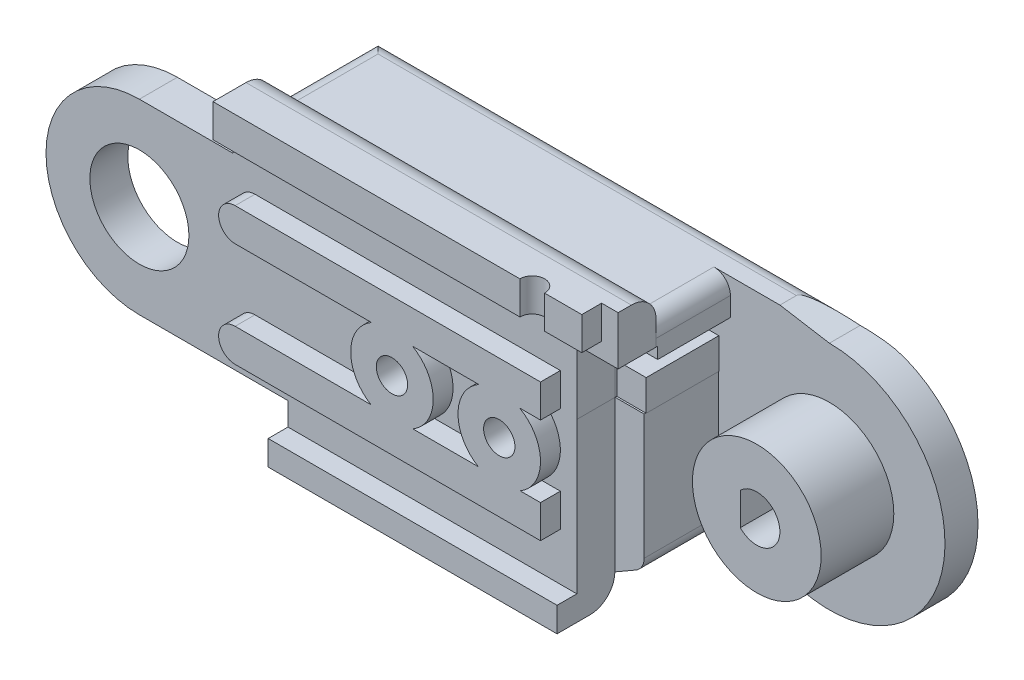
SolidWorks part; units mm, degrees
ref_plane "Front Plane" through (0, 0, 0) normal (0, 0, 1) x (1, 0, 0)
ref_plane "Top Plane" through (0, 0, 0) normal (0, 1, 0) x (1, 0, 0)
ref_plane "Right Plane" through (0, 0, 0) normal (1, 0, 0) x (0, 0, -1)
sketch "Sketch3" plane through (0, 0, 0) normal (0, 0, 1) x (1, 0, 0)
  line L7 (8, 0) -> (9, -2.5431)
  line L11 (35, 6.9569) -> (32, 7.4569)
  line L18 (5.6569, 5.6569) -> (5.6569, 7.4569)
  line L19 (5.6569, 7.4569) -> (32, 7.4569)
  line L20 (26.5, -7.0431) -> (9, -7.0431)
  line L21 (9, -7.0431) -> (9, -2.5431)
  line L23 (30.0502, -4.9929) -> (26.5, -7.0431)
  arc A4 (8, 0) -> (5.6569, 5.6569) centre (0, 0) ccw
  arc A5 (30.0502, -4.9929) -> (35, 6.9569) centre (35, -0.0431) ccw
  dimension "D3" = 3.5503
  dimension "D10" = 2.5431
  dimension "D17" = 14
  dimension "D4" = 5.6569
  dimension "D5" = 135
  dimension "D2" = 35
  dimension "D6" = 14.5
  dimension "D7" = 4.5
  dimension "D8" = 1
  dimension "D9" = 45
  dimension "D11" = 1.8
  dimension "D14" = 3
extrude "Boss-Extrude1" add sketch "Sketch3" along normal blind 2 contours A5 L11 L19 L18 A4 L7 L21 L20 L23
sketch "Sketch20" plane through (0, 0, 0) normal (0, 0, 1) x (1, 0, 0)
  line L0 (0, 7) -> (0, 7.5) construction
  line L1 (0, 7.5) -> (-19.4737, 7.5) construction
  line L2 (0, 5.3) -> (-14, 5.3) construction
  line L3 (0, 4) -> (-14, 4) construction
  line L4 (-14, 4) -> (-14, 5.3) construction
  line L5 (0, 5.3) -> (17.4849, 5.3) construction
  line L6 (17.4849, 5.3) -> (17.4849, 4) construction
  line L7 (17.4849, 4) -> (0, 4) construction
  line L8 (-2.5, 7.5) -> (-2.5, 2.868) construction
  circle A0 centre (0, 0) radius 7 construction
  circle A1 centre (0, 0) radius 3.9 construction
  circle A3 centre (0, 0) radius 5.3 construction
  circle A4 centre (0, 0) radius 4 construction
  circle A5 centre (0, 0) radius 2 construction
  dimension "D1" = 0
  dimension "D2" = 2.5
ref_plane "Plane1" through (0, 0, 2) normal (0, 0, 1) x (1, 0, 0)
sketch "Sketch4" plane through (0, 0, 2) normal (0, 0, 1) x (1, 0, 0)
  line L4 (5.6569, 5.6569) -> (5.6569, 7.5)
  line L5 (5.6569, 5.6569) -> (5.6569, 7.4569) construction
  line L6 (5.6569, 7.5) -> (26.5, 7.5)
  line L10 (8, 0) -> (9, -2.5431)
  line L11 (9, -2.5431) -> (9, -7.0431)
  line L12 (9, -7.0431) -> (26.5, -7.0431)
  line L13 (26.5, -7.0431) -> (26.5, 7.5)
  arc A0 (8, 0) -> (5.6569, 5.6569) centre (0, 0) ccw construction
  arc A3 (8, 0) -> (5.6569, 5.6569) centre (0, 0) ccw
sketch "Sketch22" plane through (0, 0, 2) normal (0, 0, 1) x (1, 0, 0)
  line L1 (5.6569, 7.4569) -> (26.5, 7.4569)
  line L6 (8, 0) -> (9, -2.5431)
  line L7 (9, -2.5431) -> (9, -7.0431)
  line L8 (9, -7.0431) -> (26.5, -7.0431)
  line L10 (26.5, 7.4569) -> (32, 7.4569)
  line L11 (32, 7.4569) -> (32, 2.1289)
  line L12 (32, 2.1289) -> (28.2751, 2.1289)
  line L13 (26.5, -7.0431) -> (28.2751, -6.018)
  line L14 (30.0502, -4.9929) -> (26.5, -7.0431) construction
  line L15 (28.2751, -6.018) -> (28.2751, 2.1289)
  line L16 (5.6569, 7.4569) -> (5.6569, 5.6569)
  arc A0 (8, 0) -> (5.6569, 5.6569) centre (0, 0) ccw
  dimension "D1" = 5.328
extrude "Boss-Extrude6" add sketch "Sketch22" along normal blind 4.5
sketch "Sketch25" plane through (0, 0, 2) normal (0, 0, 1) x (1, 0, 0)
  line L0 (0, 5.3) -> (18.0981, 5.3) construction
  line L1 (0, 4) -> (18.0981, 4) construction
  line L2 (18.0981, 4) -> (18.0981, 5.3) construction
sketch "Sketch26" plane through (0, 0, 2) normal (0, 0, 1) x (1, 0, 0)
  line L1 (18.0981, 5.3) -> (2.5301, 5.3)
  line L2 (18.0981, 4) -> (2.5301, 4)
  line L3 (2.5301, 5.3) -> (2.5301, 4)
  line L4 (18.0981, 5.3) -> (32, 5.3)
  line L5 (32, 2.1289) -> (32, 7.4569) construction
  line L6 (32, 5.3) -> (32, 4)
  line L7 (32, 4) -> (18.0981, 4)
extrude "Cut-Extrude6" cut sketch "Sketch26" along normal blind 4.5
ref_plane "Plane18" through (0, 0, 6.5) normal (0, 0, 1) x (1, 0, 0)
sketch "Sketch31" plane through (0, 0, 6.5) normal (0, 0, 1) x (1, 0, 0)
  line L0 (2.4327, 5.6569) -> (0, 5.6569)
  line L4 (9, -5.6569) -> (0, -5.6569)
  line L7 (2.4327, 5.6569) -> (5.6569, 5.6569)
  line L8 (5.6569, 5.6569) -> (5.6569, 7.4569)
  line L12 (9, -7.0431) -> (9, -5.6569)
  line L13 (9, -2.5431) -> (9, -7.0431) construction
  line L16 (32, 7.4569) -> (32, 2.1289)
  line L17 (32, 2.1289) -> (28.2751, 2.1289)
  line L22 (5.6569, 7.4569) -> (5.6569, 8.9569)
  line L23 (5.6569, 8.9569) -> (32, 8.9569)
  line L24 (32, 8.9569) -> (32, 7.4569)
  line L25 (9, -7.0431) -> (9, -8.5431)
  line L26 (9, -8.5431) -> (26.5, -8.5431)
  line L27 (26.5, -8.5431) -> (26.5, -7.0431)
  line L28 (26.5, -7.0431) -> (26.5, 2.1289)
  line L29 (26.5, 2.1289) -> (28.2751, 2.1289)
  line L30 (9, -7.0431) -> (26.5, -7.0431) construction
  line L31 (32, 7.4569) -> (5.6569, 7.4569) construction
  arc A0 (0, 5.6569) -> (0, -5.6569) centre (0, 0) ccw
  dimension "D1" = 5.6569
  dimension "D2" = 5.6569
  dimension "D3" = 1.5
  dimension "D4" = 1.5
extrude "Boss-Extrude14" add sketch "Sketch31" along normal blind 2.3 separate body
sketch "Sketch32" plane through (0, 0, 8.8) normal (0, 0, 1) x (1, 0, 0)
  circle A0 centre (0, 0) radius 3
  dimension "D1" = 6
extrude "Cut-Extrude7" cut sketch "Sketch32" against normal blind 2.3
sketch "Sketch33" plane through (0, 0, 8.8) normal (0, 0, 1) x (1, 0, 0)
  line L1 (5.6569, 8.9569) -> (5.6569, 6.9569)
  line L4 (9, -7.0431) -> (9, -8.5431)
  line L7 (7, -4.1569) -> (25.5, -4.1569)
  line L11 (9, -8.5431) -> (26.5, -8.5431)
  line L15 (26.5, -8.5431) -> (26.5, -7.0431)
  line L16 (26.5, -7.0431) -> (9, -7.0431)
  line L17 (5.6569, 8.9569) -> (28, 8.9569)
  line L18 (32, 8.9569) -> (5.6569, 8.9569) construction
  line L21 (28, 6.9569) -> (28, 8.9569)
  line L22 (25.5, -4.1569) -> (25.5, -2.1569)
  line L23 (25.5, -2.1569) -> (7, -2.1569)
  line L27 (5.6569, 6.9569) -> (28, 6.9569)
  line L28 (25.5, 2.172) -> (7, 2.172)
  line L30 (7, 4.172) -> (25.5, 4.172)
  line L33 (25.5, 2.172) -> (25.5, 4.172)
  line L34 (32, 2.1289) -> (32, 8.9569) construction
  line L35 (9, -8.5431) -> (26.5, -8.5431) construction
  line L37 (26.5, -8.5431) -> (26.5, 2.1289) construction
  arc A1 (7, -2.1569) -> (7, -4.1569) centre (7, -3.1569) ccw
  arc A2 (7, 4.172) -> (7, 2.172) centre (7, 3.172) ccw
  dimension "D1" = 1.5
  dimension "D2" = 2
  dimension "D3" = 2
  dimension "D5" = 2
  dimension "D6" = 2.5
  dimension "D8" = 4
extrude "Boss-Extrude15" add sketch "Sketch33" along normal blind 1.2
sketch "Sketch34" plane through (0, 0, 2) normal (0, 0, 1) x (1, 0, 0)
  line L0 (35, 5.3) -> (18.0981, 5.3) construction
  line L1 (35, 4) -> (18.0981, 4) construction
  circle A0 centre (35, -0.0431) radius 2 construction
  circle A1 centre (35, -0.0431) radius 5.3431 construction
  circle A2 centre (35, -0.0431) radius 4.0431 construction
sketch "Sketch35" plane through (0, 0, 8.8) normal (0, 0, 1) x (1, 0, 0)
  line L0 (32, 2.1289) -> (32, 6)
  line L1 (32, 2.1289) -> (26.5203, 2.1289)
  line L2 (32, 6) -> (26.5203, 6)
  line L3 (26.5203, 2.1289) -> (26.5203, 6)
  line L4 (32, 2.1289) -> (32, 8.9569) construction
  dimension "D1" = 5.4796
extrude "Cut-Extrude8" cut sketch "Sketch35" against normal blind 2.4
sketch "Sketch36" plane through (0, 0, 6.4) normal (0, 0, 1) x (1, 0, 0)
  line L0 (32, 2.1289) -> (32, 4)
  line L1 (32, 2.1289) -> (28.3, 2.1289)
  line L2 (32, 4) -> (28.3, 4)
  line L3 (28.3, 2.1289) -> (28.3, 4)
  line L4 (26.5, -7.0431) -> (26.5, 7.5) construction
  dimension "D1" = 1.8
extrude "Cut-Extrude9" cut sketch "Sketch36" against normal blind 4.4
sketch "Sketch37" plane through (0, 0, 2) normal (0, 0, 1) x (1, 0, 0)
  circle A0 centre (35, -0.0431) radius 3.9
  dimension "D1" = 7.8
extrude "Boss-Extrude16" add sketch "Sketch37" along normal blind 4.4
sketch "Sketch39" plane through (0, 0, 6.4) normal (0, 0, 1) x (1, 0, 0)
  line L0 (34, 0.9367) -> (34, -1.0229)
  arc A0 (34, -1.0229) -> (34, 0.9367) centre (35, -0.0431) ccw
  dimension "D2" = 2.8
  dimension "D1" = 1
extrude "Cut-Extrude10" cut sketch "Sketch39" against normal through all
sketch "Sketch43" plane through (0, 0, 8.8) normal (0, 0, 1) x (1, 0, 0)
  line L2 (0, -5.6569) -> (9, -5.6569) construction
  circle A0 centre (16.5, 0) radius 2.5
  circle A1 centre (23, 0) radius 2.5
  dimension "D1" = 7.5
  dimension "D3" = 5
  dimension "D4" = 6.5
  dimension "D2" = 5.6569
extrude "Boss-Extrude17" add sketch "Sketch43" along normal blind 1.2
sketch "Sketch44" plane through (0, 0, 10) normal (0, 0, 1) x (1, 0, 0)
  circle A0 centre (16.5, 0) radius 0.95
  circle A1 centre (23, 0) radius 0.95
  dimension "D1" = 1.9
  dimension "D2" = 1.9
extrude "Cut-Extrude11" cut sketch "Sketch44" against normal through all
sketch "Sketch45" plane through (0, 0, 0) normal (0, 0, -1) x (-1, 0, 0)
  circle A0 centre (-16.5, 0) radius 2
  circle A1 centre (-23, 0) radius 2
extrude "Cut-Extrude12" cut sketch "Sketch45" against normal blind 4.5
ref_plane "Plane17" through (0, 0, 10) normal (0, 0, 1) x (1, 0, 0)
sketch "Sketch48" plane through (0, 0, 2) normal (0, 0, 1) x (1, 0, 0)
  circle A0 centre (35, -0.0431) radius 6 construction
  dimension "D1" = 12
sketch "Sketch49" plane through (0, 6.9569, 0) normal (0, -1, 0) x (1, 0, 0)
  line L0 (5.6569, 10) -> (28, 10) construction
  line L1 (28, 10) -> (28, 8.8) construction
  line L2 (5.6569, 10) -> (5.6569, 8.8) construction
  circle A0 centre (25, 10) radius 0.75
  dimension "D1" = 3
  dimension "D3" = 1.5
  dimension "D2" = 19.3431
sketch "Sketch50" plane through (0, 0, 10) normal (0, 0, 1) x (1, 0, 0)
  line L0 (25, 6.9569) -> (27.3935, -5.0795) construction
extrude "Cut-Extrude13" cut sketch "Sketch49" against normal blind 3
sketch "Sketch51" plane through (0, 0, 8.8) normal (0, 0, 1) x (1, 0, 0)
  line L0 (32, 8.9569) -> (29, 8.9569)
  line L1 (32, 8.9569) -> (32, 4.9913)
  line L2 (29, 8.9569) -> (29, 4.9913)
  line L3 (32, 4.9913) -> (29, 4.9913)
  line L5 (32, 8.9569) -> (28, 8.9569) construction
  line L7 (32, 6) -> (32, 8.9569) construction
  dimension "D1" = 3
extrude "Cut-Extrude14" cut sketch "Sketch51" against normal blind 6.8
fillet "Fillet1" radius 1.5 2 edges at (17.3284, 8.9569, 6.5) (17.75, -8.5431, 6.5)
fillet "Fillet3" radius 1 6 edges at (28.2751, -6.018, 4.25) (29, 7.4569, 4.25) (9, -7.0431, 3.25) (5.6569, 7.4569, 3.25) (17.75, -7.0431, 0) (18.8284, 7.4569, 0)
